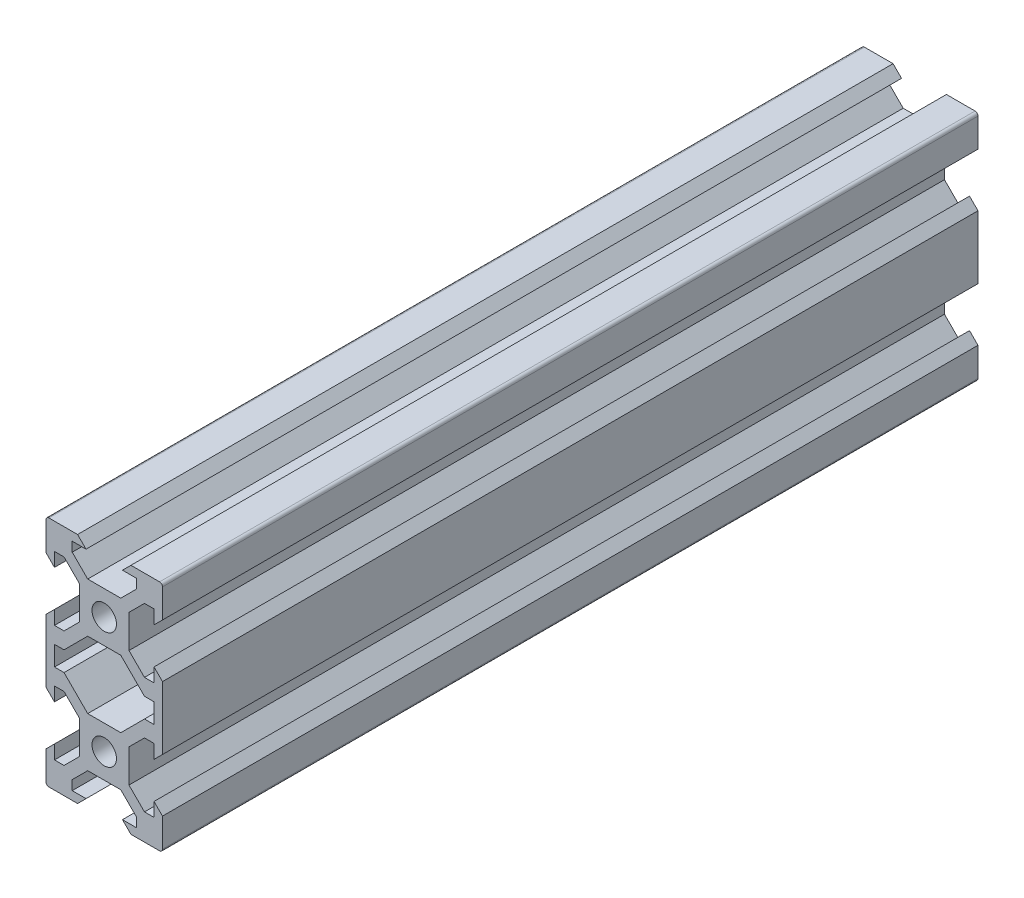
SolidWorks part; units mm, degrees
ref_plane "Front Plane" through (0, 0, 0) normal (0, 0, 1) x (1, 0, 0)
ref_plane "Top Plane" through (0, 0, 0) normal (0, 1, 0) x (1, 0, 0)
ref_plane "Right Plane" through (0, 0, 0) normal (1, 0, 0) x (0, 0, -1)
sketch "Sketch2" plane through (0, 0, 0) normal (0, 0, 1) x (1, 0, 0)
  line L0 (-4.58, -10) -> (-3.125, -8.545)
  line L1 (-9.5, -10) -> (9.5, -10)
  line L2 (-10, -9.5) -> (-10, 29.5)
  line L3 (-10, 10) -> (10, 10)
  line L4 (10, -9.5) -> (10, 29.5)
  line L5 (-10, -10) -> (10, 10) construction
  line L6 (-10, 10) -> (10, -10) construction
  line L7 (-3.125, -8.545) -> (-5.5, -8.545)
  line L8 (0, 4.8178) -> (0, -5.9385) construction
  line L9 (-8.545, 3.125) -> (-10, 4.58)
  line L10 (-8.545, 5.5) -> (-8.545, 3.125)
  line L11 (5.5, -8.545) -> (3.125, -8.545)
  line L12 (3.125, -8.545) -> (4.58, -10)
  line L13 (-3.125, -8.545) -> (3.125, -8.545) construction
  line L14 (-5.5, -8.545) -> (-5.5, -6.905)
  line L15 (-5.5, -6.905) -> (-2.84, -4.245)
  line L16 (-2.84, -4.245) -> (2.84, -4.245)
  line L17 (2.84, -4.245) -> (5.5, -6.905)
  line L18 (5.5, -6.905) -> (5.5, -8.545)
  line L19 (-6.905, 5.5) -> (-8.545, 5.5)
  line L20 (-4.245, 2.84) -> (-6.905, 5.5)
  line L21 (-10, -4.58) -> (-8.545, -3.125)
  line L22 (-8.545, -3.125) -> (-8.545, -5.5)
  line L23 (-8.545, -5.5) -> (-6.905, -5.5)
  line L24 (-6.905, -5.5) -> (-4.245, -2.84)
  line L25 (-4.245, -2.84) -> (-4.245, 2.84)
  line L26 (10, -4.58) -> (8.545, -3.125)
  line L27 (8.545, -3.125) -> (8.545, -5.5)
  line L28 (8.545, -5.5) -> (6.905, -5.5)
  line L29 (6.905, -5.5) -> (4.245, -2.84)
  line L30 (4.245, -2.84) -> (4.245, 2.84)
  line L31 (4.245, 2.84) -> (6.905, 5.5)
  line L32 (6.905, 5.5) -> (8.545, 5.5)
  line L33 (8.545, 3.125) -> (10, 4.58)
  line L34 (8.545, 5.5) -> (8.545, 3.125)
  line L35 (-3.7027, 0) -> (5.6465, 0) construction
  line L36 (-2.84, 4.245) -> (2.84, 4.245)
  line L37 (-2.84, 4.245) -> (-6.905, 8.31)
  line L38 (-6.905, 8.31) -> (-8.545, 8.31)
  line L39 (-8.545, 8.31) -> (-8.545, 11.69)
  line L40 (-8.545, 10) -> (8.545, 10)
  line L41 (8.545, 11.69) -> (8.545, 8.31)
  line L42 (8.545, 8.31) -> (6.905, 8.31)
  line L43 (6.905, 8.31) -> (2.84, 4.245)
  line L44 (-10, 4.58) -> (-10, -4.58)
  line L45 (10, 4.58) -> (10, -4.58)
  line L46 (-4.58, -10) -> (4.58, -10)
  line L47 (-3.7027, 20) -> (5.6465, 20) construction
  line L48 (-3.125, 28.545) -> (3.125, 28.545) construction
  line L49 (0, 15.1822) -> (0, 25.9385) construction
  line L50 (-10, 10) -> (10, 30) construction
  line L51 (-10, 30) -> (10, 10) construction
  line L52 (-4.58, 30) -> (4.58, 30)
  line L53 (10, 15.42) -> (10, 24.58)
  line L54 (-10, 15.42) -> (-10, 24.58)
  line L55 (6.905, 11.69) -> (2.84, 15.755)
  line L56 (8.545, 11.69) -> (6.905, 11.69)
  line L57 (-6.905, 11.69) -> (-8.545, 11.69)
  line L58 (-2.84, 15.755) -> (-6.905, 11.69)
  line L59 (-2.84, 15.755) -> (2.84, 15.755)
  line L60 (8.545, 14.5) -> (8.545, 16.875)
  line L61 (8.545, 16.875) -> (10, 15.42)
  line L62 (6.905, 14.5) -> (8.545, 14.5)
  line L63 (4.245, 17.16) -> (6.905, 14.5)
  line L64 (4.245, 22.84) -> (4.245, 17.16)
  line L65 (6.905, 25.5) -> (4.245, 22.84)
  line L66 (8.545, 25.5) -> (6.905, 25.5)
  line L67 (8.545, 23.125) -> (8.545, 25.5)
  line L68 (10, 24.58) -> (8.545, 23.125)
  line L69 (-4.245, 22.84) -> (-4.245, 17.16)
  line L70 (-6.905, 25.5) -> (-4.245, 22.84)
  line L71 (-8.545, 25.5) -> (-6.905, 25.5)
  line L72 (-8.545, 23.125) -> (-8.545, 25.5)
  line L73 (-10, 24.58) -> (-8.545, 23.125)
  line L74 (-4.245, 17.16) -> (-6.905, 14.5)
  line L75 (-6.905, 14.5) -> (-8.545, 14.5)
  line L76 (5.5, 26.905) -> (5.5, 28.545)
  line L77 (2.84, 24.245) -> (5.5, 26.905)
  line L78 (-2.84, 24.245) -> (2.84, 24.245)
  line L79 (-5.5, 26.905) -> (-2.84, 24.245)
  line L80 (-5.5, 28.545) -> (-5.5, 26.905)
  line L81 (3.125, 28.545) -> (4.58, 30)
  line L82 (5.5, 28.545) -> (3.125, 28.545)
  line L83 (-8.545, 14.5) -> (-8.545, 16.875)
  line L84 (-8.545, 16.875) -> (-10, 15.42)
  line L85 (-3.125, 28.545) -> (-5.5, 28.545)
  line L86 (-9.5, 30) -> (9.5, 30)
  line L87 (-4.58, 30) -> (-3.125, 28.545)
  circle A0 centre (0, 0) radius 2.1
  arc A1 (9.5, -10) -> (10, -9.5) centre (9.5, -9.5) ccw
  arc A2 (-9.5, -10) -> (-10, -9.5) centre (-9.5, -9.5) cw
  arc A3 (-9.5, 30) -> (-10, 29.5) centre (-9.5, 29.5) ccw
  arc A4 (9.5, 30) -> (10, 29.5) centre (9.5, 29.5) cw
  circle A5 centre (0, 20) radius 2.1
  point P15 (0, -8.545)
  point P18 (0, -4.245)
  dimension "D1" = 4.2
  dimension "D4" = 0.5
  dimension "D2" = 20
  dimension "D3" = 20
  dimension "D5" = 6.25
  dimension "D6" = 5.68
  dimension "D7" = 11
  dimension "D8" = 9.16
  dimension "D9" = 135
  dimension "D10" = 4.3
  dimension "D11" = 45
  dimension "D12" = 4.58
  dimension "D13" = 135
  dimension "D14" = 1.64
  dimension "D15" = 1.69
  dimension "D16" = 1.64
  dimension "D17" = 1.69
extrude "Boss-Extrude1" add sketch "Sketch2" along normal blind 140 contours A4 L86 L81 L82 L76 L77 L78 L79 L80 L85 L87 A3 L2 L73 L72 L71 L70 L69 L74 L75 L83 L84 L3 L39 L57 L58 L59 L55 L56 L41 L4 L61 L60 L62 L63 L64 L65 L66 L67 L68 A5 | A2 L1 L0 L7 L14 L15 L16 L17 L18 L11 L12 A1 L4 L26 L27 L28 L29 L30 L31 L32 L34 L33 L3 L41 L42 L43 L36 L37 L38 L39 L2 L9 L10 L19 L20 L25 L24 L23 L22 L21 A0
